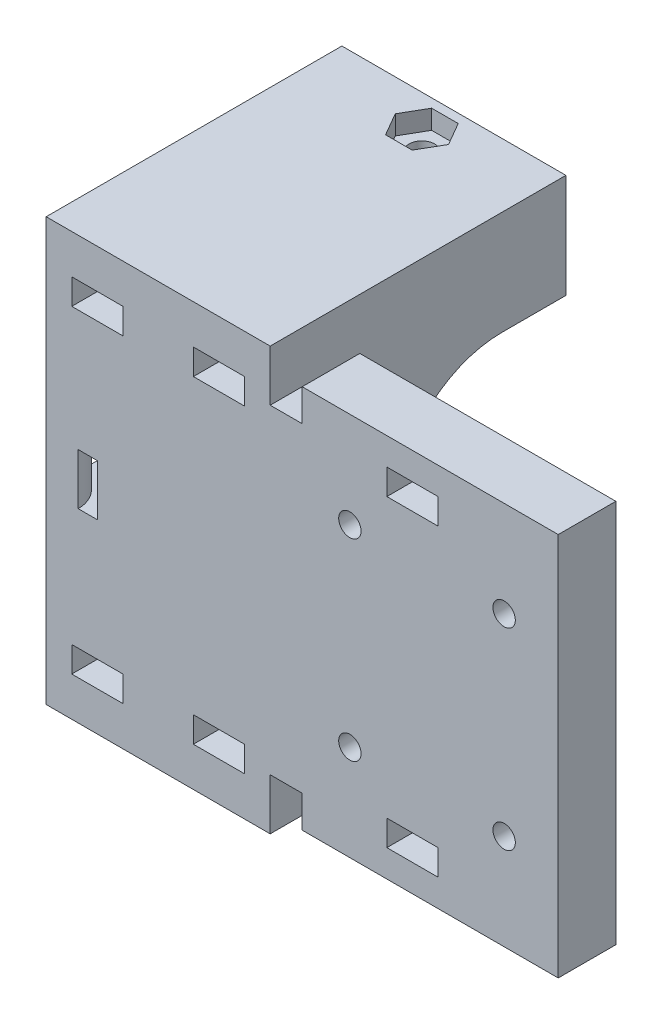
SolidWorks part; units mm, degrees
ref_plane "Front Plane" through (0, 0, 0) normal (0, 0, 1) x (1, 0, 0)
ref_plane "Top Plane" through (0, 0, 0) normal (0, 1, 0) x (1, 0, 0)
ref_plane "Right Plane" through (0, 0, 0) normal (1, 0, 0) x (0, 0, -1)
sketch "Sketch1" plane through (0, 0, 0) normal (0, 0, 1) x (1, 0, 0)
  line L1 (-97.0774, 39.75) -> (-37, 45) construction
  line L2 (3, 45) -> (-37, 45)
  line L3 (3, 45) -> (3, -45)
  line L4 (3, -45) -> (-37, -45)
  line L5 (-37, 45) -> (-37, -45)
  line L6 (3, 20) -> (3, -20) construction
  line L7 (-37, 0) -> (0, 0) construction
  dimension "D1" = 90
  dimension "D2" = 40
extrude "Boss-Extrude1" add sketch "Sketch1" along normal blind 9
sketch "Sketch2" plane through (-37, 0, 0) normal (-1, 0, 0) x (0, 0, 1)
  line L0 (9, 0) -> (0, 0) construction
  line L1 (9, 45) -> (9, -45) construction
  line L3 (0, 25) -> (9, 25)
  line L4 (0, 25) -> (0, -25)
  line L5 (0, -25) -> (9, -25)
  line L6 (9, 25) -> (9, -25)
  line L7 (0, 25) -> (9, -25) construction
  line L8 (0, -25) -> (9, 25) construction
  point P5 (4.5, 0)
  dimension "D1" = 50
extrude "Boss-Extrude2" add sketch "Sketch2" along normal blind 40
sketch "Sketch3" plane through (-77, 0, 0) normal (-1, 0, 0) x (0, 0, 1)
  line L0 (0, 25) -> (0, -25)
  line L1 (0, -25) -> (-27.2, -25)
  line L2 (-27.2, -25) -> (-27.2, -16.75)
  line L3 (-27.2, -16.75) -> (-27.2, 16.75)
  line L4 (-27.2, 16.75) -> (-27.2, 25)
  line L5 (-27.2, 25) -> (0, 25)
  circle A0 centre (-27.2, 0) radius 16.25 construction
  circle A1 centre (-27.2, 0) radius 16.25 construction
  circle A2 centre (-27.2, 0) radius 16.75
  line M9 (0, 25) -> (0, -25)
  dimension "D1" = 0.5
extrude "Boss-Extrude3" add sketch "Sketch3" against normal blind 35 contours A2 L2 L1 L5 L4 M9
sketch "Sketch4" plane through (0, 0, -27.2) normal (0, 0, -1) x (-1, 0, 0)
  line L4 (77, -25) -> (77, -16.75)
  line L5 (77, -16.75) -> (42, -16.75)
  line L6 (42, -16.75) -> (42, -25)
  line L7 (42, -25) -> (77, -25)
  line L8 (77, -25) -> (77, -16.75)
  line L9 (77, -16.75) -> (42, -16.75)
  line L10 (42, -16.75) -> (42, -25)
  line L11 (42, -25) -> (77, -25)
  line L12 (77, 16.75) -> (77, 25)
  line L13 (77, 25) -> (42, 25)
  line L14 (42, 25) -> (42, 16.75)
  line L15 (42, 16.75) -> (77, 16.75)
  line L16 (77, 16.75) -> (77, 25)
  line L17 (77, 25) -> (42, 25)
  line L18 (42, 25) -> (42, 16.75)
  line L19 (42, 16.75) -> (77, 16.75)
  dimension "D1" = 0
  dimension "D2" = 0
extrude "Boss-Extrude4" add sketch "Sketch4" along normal blind 10
sketch "Sketch5" plane through (0, -25, 0) normal (0, -1, 0) x (1, 0, 0)
  line L0 (-42, -37.2) -> (-77, -37.2) construction
  line L1 (-77, -37.2) -> (-77, 9) construction
  line L2 (-42, -37.2) -> (-77, -37.2)
  line L3 (-77, -37.2) -> (-77, 9)
  line L4 (-42, -37.2) -> (-42, 9)
  line L5 (-77, 9) -> (-37, 9) construction
  line L6 (-42, 9) -> (-77, 9)
extrude "Boss-Extrude5" add sketch "Sketch5" along normal blind 8
sketch "Sketch6" plane through (0, 25, 0) normal (0, 1, 0) x (1, 0, 0)
  line L4 (-42, 37.2) -> (-77, 37.2)
  line L5 (-77, 37.2) -> (-77, -9)
  line L6 (-77, -9) -> (-42, -9)
  line L7 (-42, -9) -> (-42, 37.2)
  line L8 (-42, 37.2) -> (-77, 37.2)
  line L9 (-77, 37.2) -> (-77, -9)
  line L10 (-77, -9) -> (-42, -9)
  line L11 (-42, -9) -> (-42, 37.2)
  dimension "D1" = 0
extrude "Boss-Extrude6" add sketch "Sketch6" along normal blind 8
sketch "Sketch8" plane through (0, -45, 0) normal (0, -1, 0) x (1, 0, 0)
  line L0 (3, 9) -> (3, 25)
  line L1 (-4.652, 29.2387) -> (-37, 9)
  line L2 (-37, 9) -> (-37, 0) construction
  line L3 (-37, 9) -> (3, 9) construction
  line L4 (-37, 9) -> (3, 9)
  arc A0 (3, 25) -> (-4.652, 29.2387) centre (-2, 25) ccw
  dimension "D2" = 5
  dimension "D1" = 16
extrude "Boss-Extrude7" [suppressed] add sketch "Sketch8" against normal blind 8
sketch "Sketch9" plane through (0, 45, 0) normal (0, 1, 0) x (1, 0, 0)
  line L3 (3, -25) -> (3, -9)
  line L4 (-37, -9) -> (-4.652, -29.2387)
  line L5 (3, -9) -> (-37, -9)
  line L6 (3, -25) -> (3, -9)
  line L7 (-37, -9) -> (-4.652, -29.2387)
  line L8 (3, -9) -> (-37, -9)
  arc A1 (-4.652, -29.2387) -> (3, -25) centre (-2, -25) ccw
  arc A2 (-4.652, -29.2387) -> (3, -25) centre (-2, -25) ccw
  dimension "D1" = 0
extrude "Boss-Extrude8" [suppressed] add sketch "Sketch9" against normal blind 8
sketch "Sketch10" plane through (0, -16.75, 0) normal (0, 1, 0) x (1, 0, 0)
  line L0 (-42, 32.2) -> (-77, 32.2) construction
  line L1 (-42, 37.2) -> (-42, 27.2) construction
  line L2 (-77, 37.2) -> (-77, 27.2) construction
  circle A0 centre (-59.5, 32.2) radius 2
  dimension "D1" = 4
extrude "Cut-Extrude1" cut sketch "Sketch10" against normal through all both and the other way through all
sketch "Sketch11" plane through (0, -16.75, 0) normal (0, 1, 0) x (1, 0, 0)
  circle A0 centre (-59.5, 32.2) radius 4.25
  dimension "D1" = 8.5
extrude "Cut-Extrude2" cut sketch "Sketch11" against normal blind 4
sketch "Sketch12" plane through (0, 16.75, 0) normal (0, -1, 0) x (1, 0, 0)
  circle A1 centre (-59.5, -32.2) radius 4.25
  circle A2 centre (-59.5, -32.2) radius 4.25
  dimension "D1" = 0
extrude "Cut-Extrude3" cut sketch "Sketch12" against normal blind 4
sketch "Sketch13" plane through (0, 0, -37.2) normal (0, 0, -1) x (-1, 0, 0)
  line L0 (77, -24.875) -> (42, -24.875) construction
  line L1 (77, -33) -> (77, -16.75) construction
  line L2 (42, -16.75) -> (42, -33) construction
  line L3 (57.5, -33) -> (61.5, -33) construction
  line L4 (73, -22.875) -> (65, -22.875)
  line L5 (73, -22.875) -> (73, -26.875)
  line L6 (73, -26.875) -> (65, -26.875)
  line L7 (65, -22.875) -> (65, -26.875)
  line L8 (73, -22.875) -> (65, -26.875) construction
  line L9 (73, -26.875) -> (65, -22.875) construction
  line L10 (54, -22.875) -> (46, -22.875)
  line L11 (54, -22.875) -> (54, -26.875)
  line L12 (54, -26.875) -> (46, -26.875)
  line L13 (46, -22.875) -> (46, -26.875)
  line L14 (54, -22.875) -> (46, -26.875) construction
  line L15 (54, -26.875) -> (46, -22.875) construction
  line L16 (57.5, -33) -> (61.5, -33)
  line L17 (0, 0) -> (77, 0) construction
  line L18 (77, -16.75) -> (77, 16.75) construction
  line L19 (73, 22.875) -> (73, 26.875)
  line L20 (73, 22.875) -> (65, 22.875)
  line L21 (65, 22.875) -> (65, 26.875)
  line L22 (73, 26.875) -> (65, 26.875)
  line L23 (54, 22.875) -> (54, 26.875)
  line L24 (54, 22.875) -> (46, 22.875)
  line L25 (46, 22.875) -> (46, 26.875)
  line L26 (54, 26.875) -> (46, 26.875)
  point P6 (69, -24.875)
  point P11 (50, -24.875)
  dimension "D1" = 8
  dimension "D2" = 4
  dimension "D3" = 4
  dimension "D4" = 4
extrude "Cut-Extrude4" cut sketch "Sketch13" against normal through all contours L23 L26 L25 L24 | L19 L22 L21 L20 | L10 L13 L12 L11 | L4 L7 L6 L5
fillet "Fillet1" radius 4 4 edges at (-69, 22.875, -37.2) (-50, -22.875, -37.2) (-69, -22.875, -37.2) (-50, 22.875, -37.2)
sketch "Sketch16" plane through (0, -33, 0) normal (0, -1, 0) x (1, 0, 0)
  line L1 (-57.4215, -28.6) -> (-61.5785, -28.6)
  line L2 (-61.5785, -28.6) -> (-63.6569, -32.2)
  line L3 (-63.6569, -32.2) -> (-61.5785, -35.8)
  line L4 (-61.5785, -35.8) -> (-57.4215, -35.8)
  line L5 (-57.4215, -35.8) -> (-55.3431, -32.2)
  line L6 (-55.3431, -32.2) -> (-57.4215, -28.6)
  circle A0 centre (-59.5, -32.2) radius 3.6 construction
  dimension "D1" = 7.2
extrude "Cut-Extrude5" cut sketch "Sketch16" against normal blind 3
sketch "Sketch17" plane through (0, 33, 0) normal (0, 1, 0) x (1, 0, 0)
  line L6 (-61.5785, 28.6) -> (-57.4215, 28.6)
  line L7 (-63.6569, 32.2) -> (-61.5785, 28.6)
  line L8 (-61.5785, 35.8) -> (-63.6569, 32.2)
  line L9 (-57.4215, 35.8) -> (-61.5785, 35.8)
  line L10 (-55.3431, 32.2) -> (-57.4215, 35.8)
  line L11 (-57.4215, 28.6) -> (-55.3431, 32.2)
  line L12 (-61.5785, 28.6) -> (-57.4215, 28.6)
  line L13 (-63.6569, 32.2) -> (-61.5785, 28.6)
  line L14 (-61.5785, 35.8) -> (-63.6569, 32.2)
  line L15 (-57.4215, 35.8) -> (-61.5785, 35.8)
  line L16 (-55.3431, 32.2) -> (-57.4215, 35.8)
  line L17 (-57.4215, 28.6) -> (-55.3431, 32.2)
  dimension "D1" = 0
extrude "Cut-Extrude6" cut sketch "Sketch17" against normal blind 3
sketch "Sketch18" plane through (0, 0, 0) normal (0, 0, -1) x (-1, 0, 0)
  circle A0 centre (5.45, 15.05) radius 1.75 construction
  circle A1 centre (5.45, 15.05) radius 1.75
  circle A2 centre (5.45, -15.05) radius 1.75 construction
  circle A3 centre (5.45, -15.05) radius 1.75
  circle A4 centre (29.55, -15.05) radius 1.75 construction
  circle A5 centre (29.55, -15.05) radius 1.75
  circle A6 centre (29.55, 15.05) radius 1.75 construction
  circle A7 centre (29.55, 15.05) radius 1.75
extrude "Cut-Extrude7" cut sketch "Sketch18" against normal blind 10
sketch "Sketch19" plane through (0, 45, 0) normal (0, 1, 0) x (1, 0, 0)
  line L4 (3, 0) -> (-37, 0)
  line L5 (-37, 0) -> (-37, -9)
  line L6 (-37, -9) -> (3, -9)
  line L7 (3, -9) -> (3, 0)
  line L8 (3, 0) -> (-37, 0)
  line L9 (-37, 0) -> (-37, -9)
  line L10 (-37, -9) -> (3, -9)
  line L11 (3, -9) -> (3, 0)
  dimension "D1" = 0
extrude "Cut-Extrude8" cut sketch "Sketch19" against normal blind 12
sketch "Sketch20" plane through (0, -45, 0) normal (0, -1, 0) x (1, 0, 0)
  line L4 (-37, 0) -> (3, 0)
  line L5 (3, 0) -> (3, 9)
  line L6 (3, 9) -> (-37, 9)
  line L7 (-37, 9) -> (-37, 0)
  line L8 (-37, 0) -> (3, 0)
  line L9 (3, 0) -> (3, 9)
  line L10 (3, 9) -> (-37, 9)
  line L11 (-37, 9) -> (-37, 0)
  dimension "D1" = 0
extrude "Cut-Extrude9" cut sketch "Sketch20" against normal blind 12
sketch "Sketch21" plane through (0, -16.75, 0) normal (0, 1, 0) x (1, 0, 0)
  line L0 (-63.75, 32.2) -> (-63.75, 37.2)
  line L1 (-77, 37.2) -> (-42, 37.2) construction
  line L2 (-63.75, 37.2) -> (-55.25, 37.2)
  line L3 (-55.25, 37.2) -> (-55.25, 32.2)
  line L4 (-55.25, 32.2) -> (-63.75, 32.2)
  circle A0 centre (-59.5, 32.2) radius 4.25 construction
  circle A1 centre (-59.5, 32.2) radius 4.25 construction
extrude "Cut-Extrude10" cut sketch "Sketch21" against normal up to surface and the other way up to surface up to face at (-59.5, -20.75, -27.95) other way up to face at (-59.5, 20.75, -36.45)
sketch "Sketch22" plane through (0, 0, 9) normal (0, 0, 1) x (1, 0, 0)
  line L1 (-23.7735, -25.75) -> (-15.7735, -25.75)
  line L2 (-23.7735, -25.75) -> (-23.7735, -21.75)
  line L3 (-23.7735, -21.75) -> (-15.7735, -21.75)
  line L4 (-15.7735, -25.75) -> (-15.7735, -21.75)
  line L5 (-23.7735, 25.75) -> (-15.7735, 25.75)
  line L6 (-23.7735, 25.75) -> (-23.7735, 21.75)
  line L7 (-23.7735, 21.75) -> (-15.7735, 21.75)
  line L8 (-15.7735, 25.75) -> (-15.7735, 21.75)
extrude "Cut-Extrude11" cut sketch "Sketch22" against normal blind 14
sketch "Sketch23" plane through (0, 0, 0) normal (0, 1, 0) x (1, 0, 0)
  line L0 (-77, 37.2) -> (-77, -9) construction
  line L1 (-77, -9) -> (-42, -9) construction
  line L2 (-77, 37.2) -> (-77, -9)
  line L3 (-77, -9) -> (-42, -9)
  circle A0 centre (-77, -9) radius 5
  circle A1 centre (-77, -9) radius 8
  dimension "D1" = 10
  dimension "D2" = 3
extrude "Cut-Extrude12" cut sketch "Sketch23" against normal blind 4 and the other way blind 4 contours L3 A1 L2 A0
sketch "Sketch25" plane through (0, 33, 0) normal (0, 1, 0) x (1, 0, 0)
  line L4 (3, -9) -> (3, 0)
  line L5 (3, 0) -> (-37, 0)
  line L6 (-37, 0) -> (-37, -9)
  line L7 (-37, -9) -> (3, -9)
  line L8 (3, -9) -> (3, 0)
  line L9 (3, 0) -> (-37, 0)
  line L10 (-37, 0) -> (-37, -9)
  line L11 (-37, -9) -> (3, -9)
  dimension "D1" = 0
extrude "Cut-Extrude13" cut sketch "Sketch25" against normal blind 3
sketch "Sketch26" plane through (0, -33, 0) normal (0, -1, 0) x (1, 0, 0)
  line L4 (-37, 9) -> (-37, 0)
  line L5 (-37, 0) -> (3, 0)
  line L6 (3, 0) -> (3, 9)
  line L7 (3, 9) -> (-37, 9)
  line L8 (-37, 9) -> (-37, 0)
  line L9 (-37, 0) -> (3, 0)
  line L10 (3, 0) -> (3, 9)
  line L11 (3, 9) -> (-37, 9)
  dimension "D1" = 0
extrude "Cut-Extrude14" cut sketch "Sketch26" against normal blind 3
